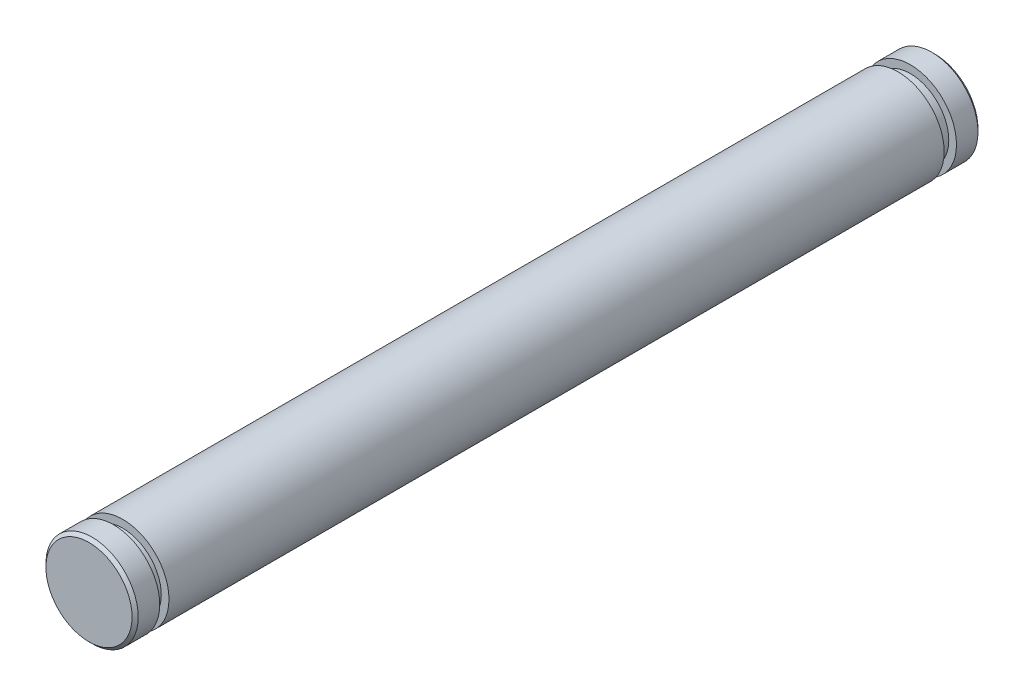
SolidWorks part; units mm, degrees
ref_plane "前视基准面" through (0, 0, 0) normal (0, 0, 1) x (1, 0, 0)
ref_plane "上视基准面" through (0, 0, 0) normal (0, 1, 0) x (1, 0, 0)
ref_plane "右视基准面" through (0, 0, 0) normal (1, 0, 0) x (0, 0, -1)
sketch "草图1" plane through (0, 0, 0) normal (0, 0, 1) x (1, 0, 0)
  circle A0 centre (0, 0) radius 1.5
  dimension "D1" = 3
extrude "凸台-拉伸1" add sketch "草图1" along normal blind 27.5
ref_plane "基准面1" through (0, 0, 0.8) normal (0, 0, 1) x (1, 0, 0)
sketch "草图2" plane through (0, 0, 0.8) normal (0, 0, 1) x (1, 0, 0)
  circle A0 centre (0, 0) radius 1.5 construction
  circle A1 centre (0, 0) radius 1.5
  circle A2 centre (0, 0) radius 1.25
  dimension "D1" = 2.5
extrude "切除-拉伸1" cut sketch "草图2" along normal blind 0.4
ref_plane "基准面2" through (0, 0, 26.7) normal (0, 0, 1) x (1, 0, 0)
sketch "草图3" plane through (0, 0, 26.7) normal (0, 0, 1) x (1, 0, 0)
  circle A0 centre (0, 0) radius 1.5 construction
  circle A1 centre (0, 0) radius 1.5
  circle A2 centre (0, 0) radius 1.25
  dimension "D1" = 2.5
extrude "切除-拉伸2" cut sketch "草图3" against normal blind 0.3
chamfer "倒角1" distance 0.1 angle 45 2 edges at (1.5, 0, 27.5) (1.5, 0, 0)
